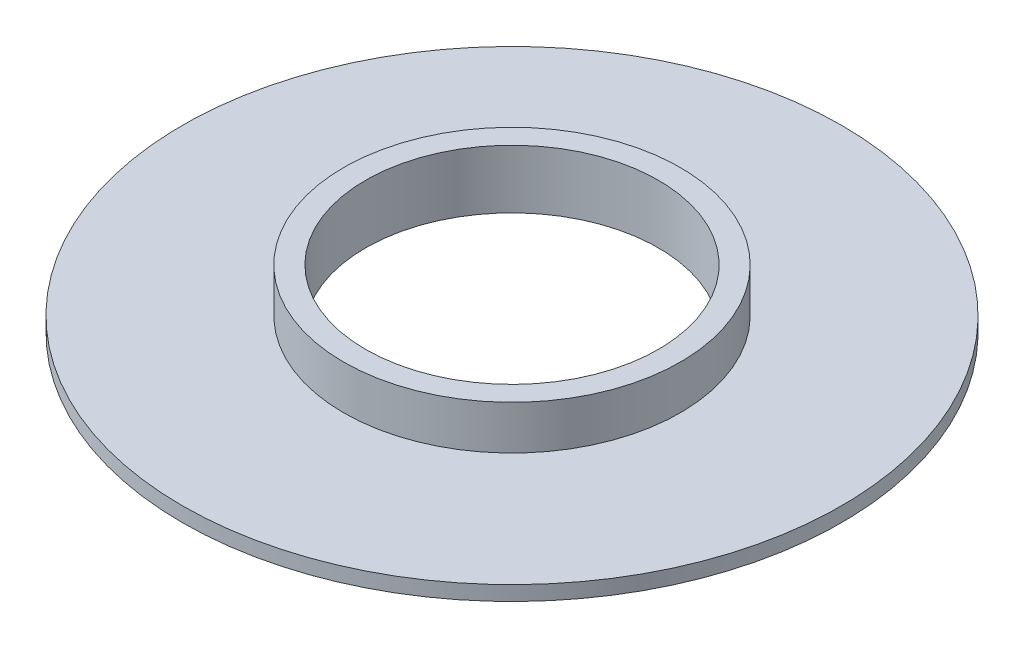
SolidWorks part; units mm, degrees
ref_plane "Plan de face" through (0, 0, 0) normal (0, 0, 1) x (1, 0, 0)
ref_plane "Plan de dessus" through (0, 0, 0) normal (0, 1, 0) x (1, 0, 0)
ref_plane "Plan de droite" through (0, 0, 0) normal (1, 0, 0) x (0, 0, -1)
sketch "Esquisse4" plane through (0, 0, 0) normal (0, 1, 0) x (1, 0, 0)
  circle A0 centre (0, 0) radius 10
  circle A1 centre (0, 0) radius 22.5
extrude "Boss.-Extru.1" add sketch "Esquisse4" along normal blind 1
sketch "Esquisse5" plane through (0, 1, 0) normal (0, 1, 0) x (1, 0, 0)
  circle A0 centre (0, 0) radius 11.5
extrude "Boss.-Extru.2" add sketch "Esquisse5" along normal blind 3
sketch "Esquisse6" plane through (0, 4, 0) normal (0, 1, 0) x (1, 0, 0)
  circle A0 centre (0, 0) radius 10
extrude "Enlèv. mat.-Extru.1" cut sketch "Esquisse6" against normal up to next
